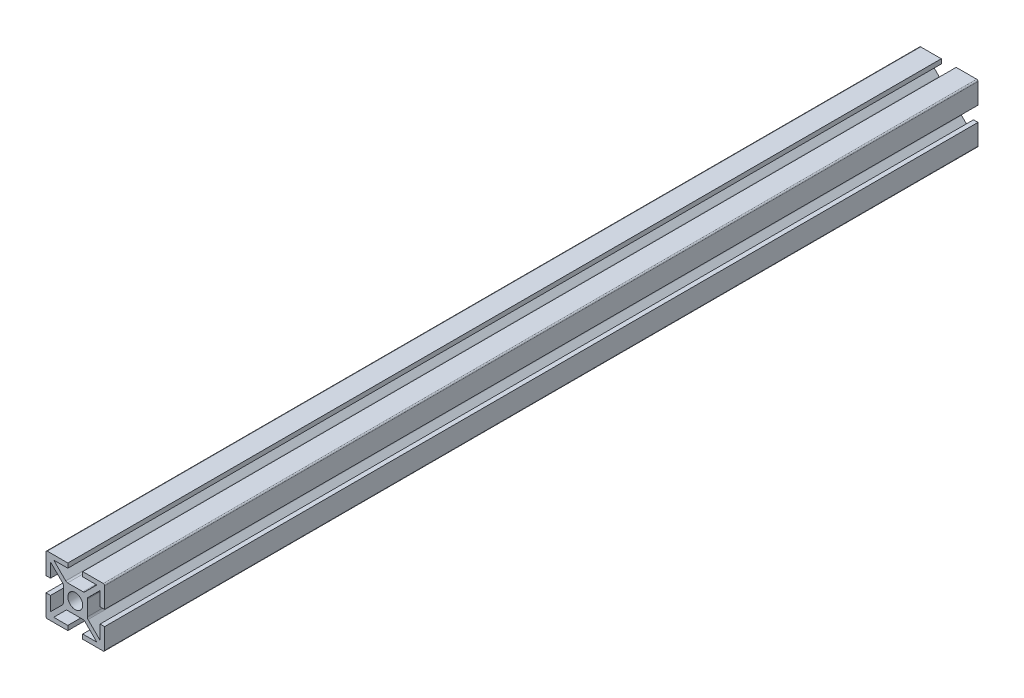
SolidWorks part; units mm, degrees
ref_plane "Plan de face" through (0, 0, 0) normal (0, 0, 1) x (1, 0, 0)
ref_plane "Plan de dessus" through (0, 0, 0) normal (0, 1, 0) x (1, 0, 0)
ref_plane "Plan de droite" through (0, 0, 0) normal (1, 0, 0) x (0, 0, -1)
sketch "Esquisse1" plane through (0, 0, 0) normal (0, 0, 1) x (1, 0, 0)
  line L0 (0, 22) -> (0, -5.6123) construction
  line L1 (-20.8753, 0) -> (5.9514, 0) construction
  line L2 (-2.8, 11) -> (-2.8, 9.3)
  line L3 (-9.3, 2.8) -> (-9.3, 8.0979)
  line L4 (-9.3, 8.0979) -> (-4.5, 3.2979)
  line L5 (-11, 2.8) -> (-11, 11)
  line L6 (-11, 11) -> (-2.8, 11)
  line L7 (-9.3, 2.8) -> (-11, 2.8)
  line L8 (-8.0979, 9.3) -> (-2.8, 9.3)
  line L9 (-8.0979, 9.3) -> (-3.2979, 4.5)
  line L10 (-3.2979, 4.5) -> (3.2979, 4.5)
  line L11 (-4.5, 3.2979) -> (-4.5, -3.2979)
  line L12 (8.0979, 9.3) -> (3.2979, 4.5)
  line L13 (8.0979, 9.3) -> (2.8, 9.3)
  line L14 (2.8, 11) -> (2.8, 9.3)
  line L15 (11, 11) -> (2.8, 11)
  line L16 (11, 2.8) -> (11, 11)
  line L17 (9.3, 2.8) -> (11, 2.8)
  line L18 (9.3, 2.8) -> (9.3, 8.0979)
  line L19 (4.5, 3.2979) -> (4.5, -3.2979)
  line L20 (9.3, 8.0979) -> (4.5, 3.2979)
  line L21 (9.3, -2.8) -> (11, -2.8)
  line L22 (9.3, -8.0979) -> (4.5, -3.2979)
  line L23 (9.3, -2.8) -> (9.3, -8.0979)
  line L24 (11, -2.8) -> (11, -11)
  line L25 (11, -11) -> (2.8, -11)
  line L26 (8.0979, -9.3) -> (3.2979, -4.5)
  line L27 (2.8, -11) -> (2.8, -9.3)
  line L28 (8.0979, -9.3) -> (2.8, -9.3)
  line L29 (-11, -11) -> (-2.8, -11)
  line L30 (-2.8, -11) -> (-2.8, -9.3)
  line L31 (-8.0979, -9.3) -> (-2.8, -9.3)
  line L32 (-3.2979, -4.5) -> (3.2979, -4.5)
  line L33 (-8.0979, -9.3) -> (-3.2979, -4.5)
  line L34 (-9.3, -8.0979) -> (-4.5, -3.2979)
  line L35 (-9.3, -2.8) -> (-9.3, -8.0979)
  line L36 (-9.3, -2.8) -> (-11, -2.8)
  line L37 (-11, -2.8) -> (-11, -11)
  point P17 (0, 4.5)
  point P27 (4.5, 0)
  point P41 (-4.5, 0)
  dimension "D1" = 11
  dimension "D2" = 11
  dimension "D3" = 2.8
  dimension "D4" = 2.8
  dimension "D5" = 1.7
  dimension "D6" = 1.7
  dimension "D7" = 1.7
  dimension "D8" = 1.7
  dimension "D9" = 4.8
  dimension "D10" = 4.8
extrude "Extrusion1" add sketch "Esquisse1" along normal blind 328
sketch "Esquisse2" plane through (0, 0, 0) normal (0, 0, -1) x (-1, 0, 0)
  circle A0 centre (0, 0) radius 2.8
  dimension "D1" = 5.6
extrude "Enlèv. mat.-Extru.1" cut sketch "Esquisse2" against normal through all
fillet "Congé1" radius 0.5 4 edges at (11, -11, 164) (-11, -11, 164) (-11, 11, 164) (11, 11, 164)
fillet "Congé2" radius 1 8 edges at (-4.5, -3.2979, 164) (-4.5, 3.2979, 164) (3.2979, -4.5, 164) (-3.2979, -4.5, 164) (4.5, -3.2979, 164) (4.5, 3.2979, 164) (-3.2979, 4.5, 164) (3.2979, 4.5, 164)
